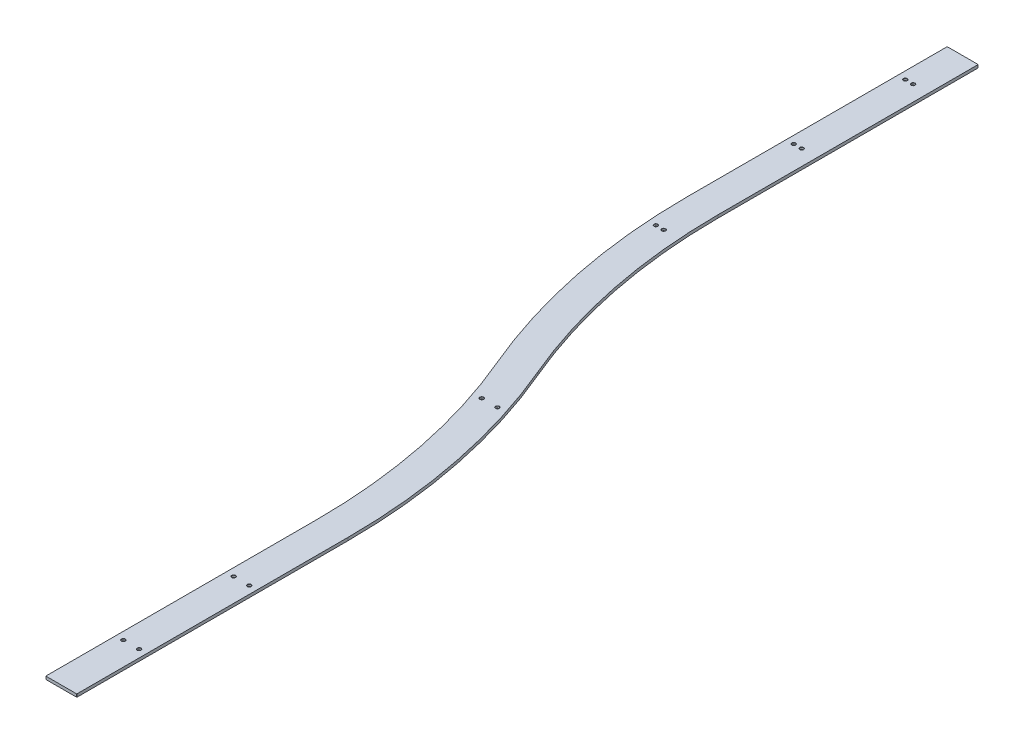
SolidWorks part; units mm, degrees
material "6061 Alloy"
ref_plane "Front" through (0, 0, 0) normal (0, 0, 1) x (1, 0, 0)
ref_plane "Top" through (0, 0, 0) normal (0, 1, 0) x (1, 0, 0)
ref_plane "Right" through (0, 0, 0) normal (1, 0, 0) x (0, 0, -1)
sketch "Sketch1" plane through (0, 0, 0) normal (0, 1, 0) x (1, 0, 0)
  line L0 (0, 74.1) -> (0, 950)
  line L1 (-304.8, 2450) -> (-304.8, 3290)
  line L2 (0, 0) -> (0, 74.1) construction
  arc A0 (0, 950) -> (-152.4, 1700) centre (-1921.6724, 950) ccw
  arc A1 (-304.8, 2450) -> (-152.4, 1700) centre (1616.8724, 2450) ccw
  dimension "D1" = 875.9
  dimension "D2" = 1500
  dimension "D3" = 840
  dimension "D4" = 304.8
  dimension "D5" = 74.1
extrude "Extrude-Thin1" add sketch "Sketch1" along normal blind 9.525 thin thin type mid plane wall 100
fillet "Fillet1" radius 1 4 edges at (-354.8, 4.7625, -3290) (-254.8, 4.7625, -3290) (50, 4.7625, -74.1) (-50, 4.7625, -74.1)
sketch "Sketch2" plane through (0, 9.525, 0) normal (0, 1, 0) x (1, 0, 0)
  line L0 (-304.8, 3130) -> (-304.8, 3104.6) construction
  line L1 (0, 0) -> (148.0994, 0) construction
  line L2 (-330.2, 3142.7) -> (-330.2, 3117.3)
  line L3 (-354.8, 3130) -> (-254.8, 3130)
  line L4 (-279.4, 3142.7) -> (-279.4, 3117.3)
  line L5 (-354.8, 2450) -> (-354.8, 3289) construction
  line L6 (-254.8, 2450) -> (-254.8, 3289) construction
  line L7 (-353.8, 3290) -> (-255.8, 3290) construction
  line L8 (-354.8, 2770) -> (-254.8, 2770) construction
  line L9 (-350.5096, 2320) -> (-250.2799, 2320) construction
  line L10 (-150.4772, 1555) -> (-45.1152, 1555) construction
  line L11 (-325.7947, 2320) -> (-274.9947, 2320)
  line L12 (-123.1962, 1555) -> (-72.3962, 1555)
  line L13 (-50, 656.05) -> (50, 656.05) construction
  line L14 (-50, 75.1) -> (-50, 950) construction
  line L15 (50, 75.1) -> (50, 950) construction
  line L16 (-25.4, 656.05) -> (25.4, 656.05)
  line L17 (-50, 300) -> (50, 300) construction
  line L18 (-25.4, 300) -> (25.4, 300)
  arc A3 (-354.8, 2450) -> (-198.4347, 1680.4857) centre (1616.8724, 2450) ccw construction
  arc A4 (-254.8, 2450) -> (-106.3653, 1719.5143) centre (1616.8724, 2450) ccw construction
  arc A5 (-50, 950) -> (-198.4347, 1680.4857) centre (-1921.6724, 950) ccw construction
  arc A6 (50, 950) -> (-106.3653, 1719.5143) centre (-1921.6724, 950) ccw construction
  point P17 (-279.4, 3130)
  point P18 (-279.4, 2770)
  point P19 (-330.2, 2770)
  point P41 (-97.7962, 1555)
  point P50 (0, 656.05)
  point P55 (0, 300)
  point P58 (-304.8, 2770)
  point P60 (-300.3947, 2320)
  dimension "D1" = 50.8
  dimension "D2" = 25.4
  dimension "D3" = 160
  dimension "D4" = 520
  dimension "D5" = 50.8
  dimension "D6" = 2633.95
  dimension "D7" = 970
  dimension "D8" = 1735
  dimension "D9" = 2990
hole_wizard "CBORE for 1/4 Socket Head Cap Screw3" positions "Sketch8" profile "Sketch7" counterbore size "1/4" standard "Ansi Inch" end condition through all
sketch "Sketch8" plane through (0, 9.525, 0) normal (0, 1, 0) x (-1, 0, 0)
  line L0 (354.8, -3130) -> (254.8, -3130) construction
  line L1 (330.2, -3142.7) -> (330.2, -3117.3) construction
  point P3 (304.8, -3130)
  point P6 (330.2, -3130)
  point P8 (304.8, -2770)
  point P11 (330.2, -2770)
  point P14 (300.3947, -2320)
  point P17 (325.7947, -2320)
  point P20 (72.3962, -1555)
  point P23 (123.1962, -1555)
  point P26 (-25.4, -656.05)
  point P29 (25.4, -656.05)
  point P32 (-25.4, -300)
  point P35 (25.4, -300)
sketch "Sketch7" plane through (-304.8, 9.525, -3130) normal (1, 0, 0) x (0, 0, 1)
  line L0 (0, 0) -> (0, 9.525)
  line L1 (3.3782, 8.89) -> (4.0132, 9.525)
  line L2 (5.5562, 6.35) -> (3.3782, 6.35)
  line L3 (3.3782, 6.35) -> (3.3782, 8.89)
  line L5 (5.5562, 6.35) -> (5.5562, 0.635)
  line L6 (5.5562, 0.635) -> (6.1913, 0)
  line L7 (6.1913, 0) -> (0, 0)
  line L8 (-5.5562, 0.635) -> (-6.1913, 0) construction
  line L11 (0, -6.35) -> (0, 107.95) construction
  line L12 (4.0132, 9.525) -> (0, 9.525)
  line L13 (-3.3782, 8.89) -> (-4.0132, 9.525) construction
  dimension "Thru Hole Dia." = 6.7564
  dimension "Thru Hole Depth" = 9.525
  dimension "C'Bore Dia." = 11.1125
  dimension "C'Bore Depth" = 6.35
  dimension "Near C'Sink Dia." = 12.3825
  dimension "Near C'Sink Angle" = 90
  dimension "Far C'Sink Dia." = 8.0264
  dimension "Far C'Sink Angle" = 90
